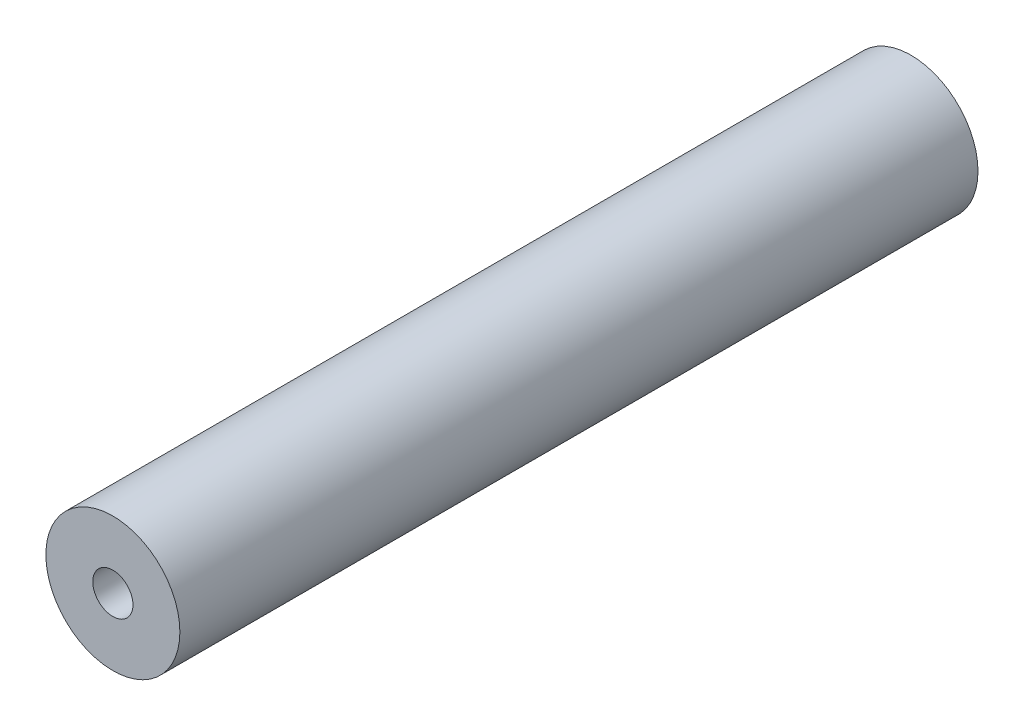
SolidWorks part; units mm, degrees
ref_plane "Front Plane" through (0, 0, 0) normal (0, 0, 1) x (1, 0, 0)
ref_plane "Top Plane" through (0, 0, 0) normal (0, 1, 0) x (1, 0, 0)
ref_plane "Right Plane" through (0, 0, 0) normal (1, 0, 0) x (0, 0, -1)
sketch "Sketch1" plane through (0, 0, 0) normal (0, 0, 1) x (1, 0, 0)
  circle A0 centre (0, 0) radius 31.75
  circle A1 centre (0, 0) radius 9.525
  dimension "D1" = 63.5
  dimension "D2" = 19.05
extrude "Boss-Extrude1" add sketch "Sketch1" along normal blind 378.206
